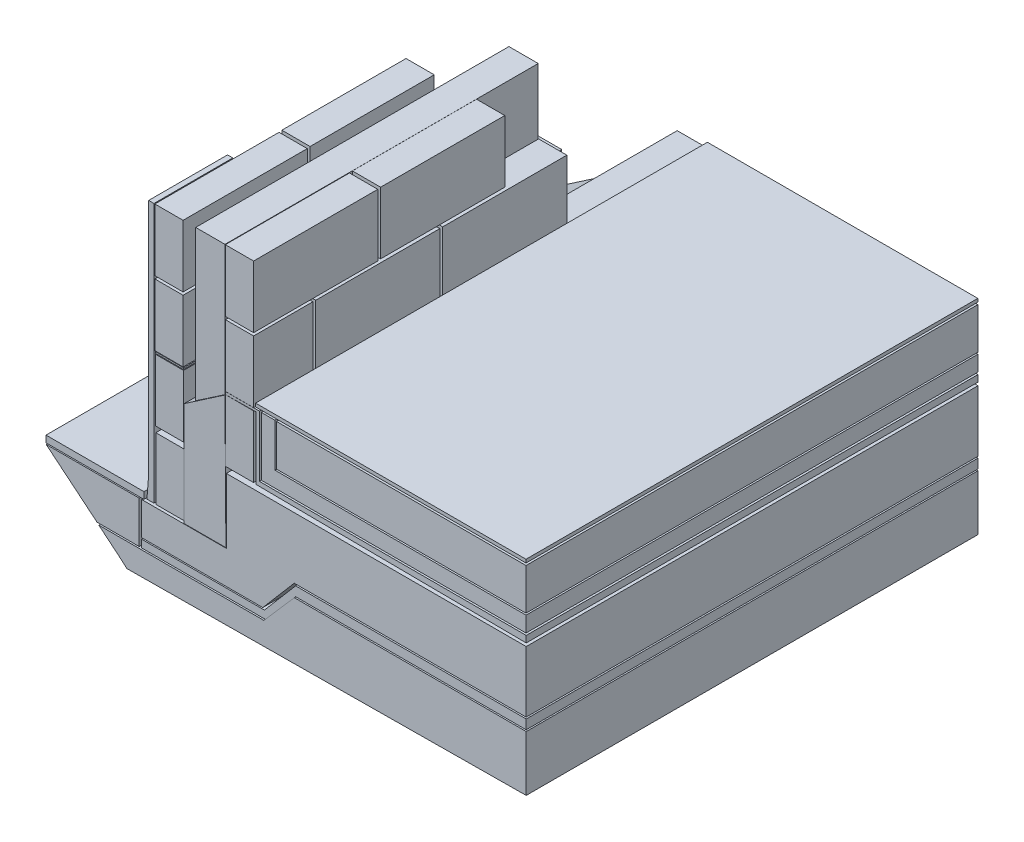
SolidWorks part; units mm, degrees
ref_plane "Front Plane" through (0, 0, 0) normal (0, 0, 1) x (1, 0, 0)
ref_plane "Top Plane" through (0, 0, 0) normal (0, 1, 0) x (1, 0, 0)
ref_plane "Right Plane" through (0, 0, 0) normal (1, 0, 0) x (0, 0, -1)
sketch "Sketch1" plane through (0, 0, 0) normal (0, 0, 1) x (1, 0, 0)
  line L0 (0, 0) -> (26.1262, -22.8216)
  line L1 (26.1262, -22.8216) -> (1435.8063, -11.4108)
  line L2 (1435.8063, 184.6868) -> (1440.9992, 184.6868)
  line L3 (1435.8063, 184.6868) -> (619.4928, 184.6868)
  line L4 (619.4928, 184.6868) -> (511.4023, 60.9451)
  line L5 (511.4023, 60.9451) -> (-73.6897, 60.9451)
  line L6 (-73.6897, 60.9451) -> (0, 0)
  line L7 (1440.9992, 184.6868) -> (1440.9992, -11.4108)
  line L8 (1440.9992, -11.4108) -> (1435.8063, -11.4108)
extrude "Extrude1" add sketch "Sketch1" against normal blind 1601
sketch "Sketch6" plane through (0, 0, 0) normal (0, 0, 1) x (1, 0, 0)
  line L0 (1440.9992, 228.8878) -> (1440.9992, 445.5033)
  line L1 (1440.9992, 445.5033) -> (378.3669, 445.5033)
  line L2 (378.3669, 445.5033) -> (378.3669, 215.5033)
  line L3 (378.3669, 215.5033) -> (78.3669, 215.5033)
  line L4 (78.3669, 215.5033) -> (78.3669, 98.3177)
  line L5 (78.3669, 98.3177) -> (507.434, 98.3177)
  line L6 (507.434, 98.3177) -> (618.9465, 228.8878)
  line L7 (618.9465, 228.8878) -> (1440.9992, 228.8878)
  line L8 (1440.9992, -11.4108) -> (1440.9992, 184.6868) construction
  dimension "D1" = 230
  dimension "D2" = 300
  dimension "D3" = 216.6155
extrude "Extrude4" add sketch "Sketch6" against normal up to vertex (1601 mm away) separate body
sketch "Sketch7" plane through (0, 0, 0) normal (0, 0, 1) x (1, 0, 0)
  line L0 (78.3669, 93.569) -> (513.2966, 93.569)
  line L1 (513.2966, 93.569) -> (624.0551, 223.2375)
  line L2 (624.0551, 223.2375) -> (1440.9992, 223.2375)
  line L3 (1440.9992, 223.2375) -> (1440.9992, 190.0192)
  line L4 (1440.9992, 190.0192) -> (624.0551, 190.0192)
  line L5 (624.0551, 190.0192) -> (518.7637, 66.7513)
  line L6 (518.7637, 66.7513) -> (78.3669, 66.7513)
  line L7 (78.3669, 66.7513) -> (78.3669, 93.569)
  line L9 (1440.9992, -11.4108) -> (1440.9992, 184.6868) construction
  line L10 (78.3669, 215.5033) -> (78.3669, 98.3177) construction
extrude "Extrude5" add sketch "Sketch7" against normal up to vertex (1601 mm away) separate body
sketch "Sketch8" plane through (0, 0, 0) normal (0, 0, 1) x (1, 0, 0)
  line L0 (378.3669, 215.5033) -> (78.3669, 215.5033) construction
  line L1 (128.3669, 445.5033) -> (228.3669, 445.5033)
  line L2 (128.3669, 445.5033) -> (128.3669, 225.5033)
  line L3 (128.3669, 225.5033) -> (228.3669, 225.5033)
  line L4 (228.3669, 445.5033) -> (228.3669, 225.5033)
  line L5 (378.3669, 445.5033) -> (378.3669, 215.5033) construction
  dimension "D1" = 100
  dimension "D2" = 220
  dimension "D3" = 10
  dimension "D4" = 150
extrude "Extrude6" add sketch "Sketch8" against normal blind 210 separate body
sketch "Sketch9" plane through (0, 0, 0) normal (0, 0, 1) x (1, 0, 0)
  line L1 (126.7181, 465.6969) -> (226.7181, 465.6969)
  line L2 (126.7181, 465.6969) -> (126.7181, 685.6969)
  line L3 (126.7181, 685.6969) -> (226.7181, 685.6969)
  line L4 (226.7181, 465.6969) -> (226.7181, 685.6969)
  line L5 (375.0647, 465.6969) -> (475.0647, 465.6969)
  line L6 (375.0647, 465.6969) -> (375.0647, 685.6969)
  line L7 (375.0647, 685.6969) -> (475.0647, 685.6969)
  line L8 (475.0647, 465.6969) -> (475.0647, 685.6969)
  dimension "D1" = 220
  dimension "D2" = 100
  dimension "D3" = 100
  dimension "D4" = 220
extrude "Extrude7" add sketch "Sketch9" against normal blind 440 separate body
sketch "Sketch10" plane through (0, 0, 0) normal (0, 0, 1) x (1, 0, 0)
  line L0 (226.7181, 685.6969) -> (126.7181, 685.6969) construction
  line L1 (125.1519, 695.6969) -> (225.1519, 695.6969)
  line L2 (125.1519, 695.6969) -> (125.1519, 915.6969)
  line L3 (125.1519, 915.6969) -> (225.1519, 915.6969)
  line L4 (225.1519, 695.6969) -> (225.1519, 915.6969)
  line L5 (375.0647, 695.6969) -> (475.0647, 695.6969)
  line L6 (375.0647, 695.6969) -> (375.0647, 915.6969)
  line L7 (375.0647, 915.6969) -> (475.0647, 915.6969)
  line L8 (475.0647, 695.6969) -> (475.0647, 915.6969)
  line L9 (475.0647, 685.6969) -> (375.0647, 685.6969) construction
  line L10 (475.0647, 465.6969) -> (475.0647, 685.6969) construction
  dimension "D1" = 100
  dimension "D2" = 220
  dimension "D3" = 220
  dimension "D4" = 100
  dimension "D5" = 10
  dimension "D6" = 10
extrude "Extrude8" add sketch "Sketch10" against normal blind 210 separate body
sketch "Sketch11" plane through (0, 0, 0) normal (0, 0, 1) x (1, 0, 0)
  line L0 (225.1519, 915.6969) -> (125.1519, 915.6969) construction
  line L1 (125.1519, 925.6969) -> (225.1519, 925.6969)
  line L2 (125.1519, 925.6969) -> (125.1519, 1145.6969)
  line L3 (125.1519, 1145.6969) -> (225.1519, 1145.6969)
  line L4 (225.1519, 925.6969) -> (225.1519, 1145.6969)
  line L5 (374.776, 925.6969) -> (474.776, 925.6969)
  line L6 (374.776, 925.6969) -> (374.776, 1145.6969)
  line L7 (374.776, 1145.6969) -> (474.776, 1145.6969)
  line L8 (474.776, 925.6969) -> (474.776, 1145.6969)
  line L9 (475.0647, 915.6969) -> (375.0647, 915.6969) construction
  dimension "D1" = 220
  dimension "D2" = 100
  dimension "D3" = 100
  dimension "D4" = 220
  dimension "D5" = 10
  dimension "D6" = 10
extrude "Extrude9" add sketch "Sketch11" against normal blind 440 separate body
sketch "Sketch12" plane through (128.3669, 0, 0) normal (-1, 0, 0) x (0, 0, 1)
  line L0 (-1601, 445.5033) -> (0, 445.5033) construction
  line L1 (-220, 445.5033) -> (-660, 445.5033)
  line L2 (-220, 445.5033) -> (-220, 225.5033)
  line L3 (-220, 225.5033) -> (-660, 225.5033)
  line L4 (-660, 445.5033) -> (-660, 225.5033)
  line L5 (-210, 445.5033) -> (-210, 225.5033) construction
  line L6 (-670, 445.5033) -> (-1110, 445.5033)
  line L7 (-670, 445.5033) -> (-670, 225.5033)
  line L8 (-670, 225.5033) -> (-1110, 225.5033)
  line L9 (-1110, 445.5033) -> (-1110, 225.5033)
  point P10 (-210, 335.5033)
  dimension "D1" = 440
  dimension "D2" = 220
  dimension "D3" = 10
  dimension "D4" = 440
  dimension "D5" = 220
  dimension "D6" = 10
extrude "Extrude10" add sketch "Sketch12" against normal blind 100 separate body
sketch "Sketch13" plane through (126.7181, 0, 0) normal (-1, 0, 0) x (0, 0, 1)
  line L0 (-440, 685.6969) -> (-440, 465.6969) construction
  line L1 (-450, 685.9842) -> (-890, 685.9842)
  line L2 (-450, 685.9842) -> (-450, 465.9842)
  line L3 (-450, 465.9842) -> (-890, 465.9842)
  line L4 (-890, 685.9842) -> (-890, 465.9842)
  line L5 (-900, 685.6969) -> (-1340, 685.6969)
  line L6 (-900, 685.6969) -> (-900, 465.6969)
  line L7 (-900, 465.6969) -> (-1340, 465.6969)
  line L8 (-1340, 685.6969) -> (-1340, 465.6969)
  line L9 (-440, 465.6969) -> (0, 465.6969) construction
  dimension "D1" = 440
  dimension "D2" = 220
  dimension "D3" = 220
  dimension "D4" = 440
  dimension "D5" = 10
  dimension "D6" = 10
extrude "Extrude11" add sketch "Sketch13" against normal blind 100 separate body
sketch "Sketch14" plane through (128.3669, 0, 0) normal (-1, 0, 0) x (0, 0, 1)
  line L0 (-1601, 445.5033) -> (0, 445.5033) construction
  line L1 (-1120, 445.5033) -> (-1560, 445.5033)
  line L2 (-1120, 445.5033) -> (-1120, 225.5033)
  line L3 (-1120, 225.5033) -> (-1560, 225.5033)
  line L4 (-1560, 445.5033) -> (-1560, 225.5033)
  line L5 (-1110, 445.5033) -> (-1110, 225.5033) construction
  dimension "D1" = 220
  dimension "D2" = 440
  dimension "D3" = 10
extrude "Extrude12" add sketch "Sketch14" against normal blind 100 separate body
sketch "Sketch15" plane through (125.1519, 0, 0) normal (-1, 0, 0) x (0, 0, 1)
  line L0 (-210, 915.6969) -> (-210, 695.6969) construction
  line L1 (-220, 915.274) -> (-660, 915.274)
  line L2 (-220, 915.274) -> (-220, 695.274)
  line L3 (-220, 695.274) -> (-660, 695.274)
  line L4 (-660, 915.274) -> (-660, 695.274)
  line L5 (-670, 915.5026) -> (-1110, 915.5026)
  line L6 (-670, 915.5026) -> (-670, 695.5026)
  line L7 (-670, 695.5026) -> (-1110, 695.5026)
  line L8 (-1110, 915.5026) -> (-1110, 695.5026)
  dimension "D1" = 220
  dimension "D2" = 440
  dimension "D3" = 440
  dimension "D4" = 220
  dimension "D5" = 10
  dimension "D6" = 10
extrude "Extrude13" add sketch "Sketch15" against normal blind 100 separate body
sketch "Sketch16" plane through (125.1519, 0, 0) normal (-1, 0, 0) x (0, 0, 1)
  line L0 (-440, 1145.6969) -> (-440, 925.6969) construction
  line L1 (-450, 1147.2011) -> (-890, 1147.2011)
  line L2 (-450, 1147.2011) -> (-450, 927.2011)
  line L3 (-450, 927.2011) -> (-890, 927.2011)
  line L4 (-890, 1147.2011) -> (-890, 927.2011)
  dimension "D1" = 440
  dimension "D2" = 220
  dimension "D3" = 10
extrude "Extrude14" add sketch "Sketch16" against normal blind 100 separate body
sketch "Sketch17" plane through (475.0647, 0, 0) normal (1, 0, 0) x (0, 0, -1)
  line L0 (890, 465.9842) -> (450, 465.9842) construction
  line L1 (450, 685.9842) -> (890, 685.9842)
  line L2 (450, 685.9842) -> (450, 465.9842)
  line L3 (450, 465.9842) -> (890, 465.9842)
  line L4 (890, 685.9842) -> (890, 465.9842)
  line L5 (440, 925.6969) -> (440, 1145.6969) construction
  line L6 (1340, 685.6969) -> (900, 685.6969)
  line L7 (1340, 685.6969) -> (1340, 465.6969)
  line L8 (1340, 465.6969) -> (900, 465.6969)
  line L9 (900, 685.6969) -> (900, 465.6969)
  line L10 (1110, 915.5026) -> (670, 915.5026)
  line L11 (1110, 915.5026) -> (1110, 695.5026)
  line L12 (1110, 695.5026) -> (670, 695.5026)
  line L13 (670, 915.5026) -> (670, 695.5026)
  line L14 (660, 915.274) -> (220, 915.274)
  line L15 (660, 915.274) -> (660, 695.274)
  line L16 (660, 695.274) -> (220, 695.274)
  line L17 (220, 915.274) -> (220, 695.274)
  line L18 (0, 915.6969) -> (210, 915.6969)
  line L19 (0, 915.6969) -> (0, 695.6969)
  line L20 (0, 695.6969) -> (210, 695.6969)
  line L21 (210, 915.6969) -> (210, 695.6969)
  line L22 (0, 1145.6969) -> (440, 1145.6969)
  line L23 (0, 1145.6969) -> (0, 925.6969)
  line L24 (0, 925.6969) -> (440, 925.6969)
  line L25 (440, 1145.6969) -> (440, 925.6969)
  line L27 (890, 1147.2011) -> (450, 1147.2011)
  line L28 (890, 1147.2011) -> (890, 927.2011)
  line L29 (890, 927.2011) -> (450, 927.2011)
  line L30 (450, 1147.2011) -> (450, 927.2011)
extrude "Extrude15" add sketch "Sketch17" against normal blind 100
sketch "Sketch18" plane through (0, 0, 0) normal (0, 0, 1) x (1, 0, 0)
  line L0 (69.7561, 66.7513) -> (69.7561, 215.2631)
  line L1 (69.7561, 215.2631) -> (-260.0365, 215.2631)
  line L4 (69.7561, 66.7513) -> (-79.7988, 66.7513)
  line L5 (-79.7988, 66.7513) -> (-260.0365, 215.2631)
extrude "Extrude19" add sketch "Sketch18" against normal up to vertex (1601 mm away) separate body
sketch "Sketch19" plane through (0, 0, 0) normal (0, 0, 1) x (1, 0, 0)
  line L0 (1440.9992, 456.5257) -> (483.0875, 464.3663)
  line L1 (483.0875, 464.3663) -> (483.0875, 626.7546)
  line L2 (483.0875, 626.7546) -> (483.0875, 686.9511)
  line L3 (495.4208, 626.7546) -> (495.4208, 479.7829)
  line L4 (495.4208, 479.7829) -> (1440.9992, 479.7829)
  line L5 (1440.9992, 479.7829) -> (1440.9992, 456.5257)
  line L6 (483.0875, 686.9511) -> (375.0647, 685.9842)
  line L7 (375.0647, 685.9842) -> (475.0647, 685.9842) construction
  line L8 (375.0647, 685.9842) -> (375.0647, 695.274)
  line L9 (375.0647, 695.274) -> (475.0647, 695.274) construction
  line L10 (375.0647, 695.274) -> (495.4208, 695.274)
  line L11 (495.4208, 695.274) -> (495.4208, 626.7546)
extrude "Extrude20" add sketch "Sketch19" against normal up to vertex (1601 mm away) separate body
sketch "Sketch21" plane through (0, 0, 0) normal (0, 0, 1) x (1, 0, 0)
  line L0 (502.237, 694.7532) -> (502.237, 486.5906)
  line L1 (502.237, 486.5906) -> (1440.3276, 486.5906)
  line L2 (1440.3276, 486.5906) -> (1440.3276, 541.5816)
  line L3 (1440.3276, 541.5816) -> (550.4417, 541.5816)
  line L4 (550.4417, 541.5816) -> (550.4417, 694.7532)
  line L5 (550.4417, 694.7532) -> (502.237, 694.7532)
extrude "Extrude22" add sketch "Sketch21" against normal up to vertex (1601 mm away) separate body
sketch "Sketch22" plane through (0, 0, 0) normal (0, 0, 1) x (1, 0, 0)
  line L1 (556.0644, 693.8804) -> (1440.3276, 693.8804)
  line L2 (556.0644, 693.8804) -> (556.0644, 547.6191)
  line L3 (556.0644, 547.6191) -> (1440.3276, 547.6191)
  line L4 (1440.3276, 693.8804) -> (1440.3276, 547.6191)
extrude "Extrude23" add sketch "Sketch22" against normal up to vertex (1601 mm away) separate body
sketch "Sketch23" plane through (0, 0, 0) normal (0, 0, 1) x (1, 0, 0)
  line L0 (126.9611, 693.8146) -> (226.6355, 693.8146)
  line L1 (226.6355, 688.5559) -> (126.9611, 688.5559)
  line L2 (126.9611, 688.5559) -> (126.9611, 693.8146)
  line L3 (226.6355, 693.8146) -> (226.6355, 688.5559)
extrude "Extrude24" add sketch "Sketch23" against normal up to vertex (1340 mm away) separate body
sketch "Sketch24" plane through (0, 0, 0) normal (0, 0, 1) x (1, 0, 0)
  line L0 (373.4692, 683.6938) -> (376.8644, 216.962)
  line L1 (376.8644, 216.962) -> (229.0389, 216.962)
  line L2 (229.0389, 216.962) -> (229.0389, 585.0243)
  line L3 (229.0389, 585.0243) -> (373.4692, 683.6938)
extrude "Extrude25" add sketch "Sketch24" against normal up to vertex (1340 mm away) separate body
sketch "Sketch25" plane through (0, 0, 0) normal (0, 0, 1) x (1, 0, 0)
  line L0 (373.6168, 684.8576) -> (373.6168, 1146.1606)
  line L1 (373.6168, 1146.1606) -> (269.7986, 1146.1606)
  line L2 (269.7986, 1146.1606) -> (269.7986, 614.1422)
  line L3 (269.7986, 614.1422) -> (373.6168, 684.8576)
extrude "Extrude26" add sketch "Sketch25" against normal up to vertex (1110 mm away) separate body
sketch "Sketch27" plane through (0, 0, 0) normal (0, 0, 1) x (1, 0, 0)
  line L0 (121.9766, 1145.7702) -> (121.9766, 225.9237)
  line L1 (121.9766, 225.9237) -> (96.9728, 225.9237)
  line L2 (96.9728, 225.9237) -> (103.2208, 304.0239)
  line L3 (103.2208, 304.0239) -> (103.2208, 1145.7702)
  line L4 (103.2208, 1145.7702) -> (121.9766, 1145.7702)
extrude "Extrude29" add sketch "Sketch27" against normal blind 559 separate body
sketch "Sketch30" plane through (103.2208, 0, 0) normal (-1, 0, 0) x (0, 0, 1)
  line L0 (-559, 1145.7702) -> (-279.5, 1145.7702)
  line L1 (-559, 1145.7702) -> (0, 1145.7702) construction
  line L2 (-559, 225.9237) -> (0, 225.9237) construction
  line L3 (-470.8496, 225.9237) -> (-559, 225.9237)
  line L4 (-559, 225.9237) -> (-559, 1145.7702)
  spline S0 degree 3 poles (-279.5, 1145.7702) (-3.1177, 751.9861) (-620.5924, 618.2023) (-470.8496, 225.9237) knots 0 0 0 0 1 1 1 1
extrude "Extrude33" cut sketch "Sketch30" against normal mid plane 43
sketch "Sketch31" plane through (0, 0, 0) normal (0, 0, 1) x (1, 0, 0)
  line L1 (-260.6289, 219.8093) -> (86.3841, 219.8093)
  line L2 (-260.6289, 219.8093) -> (-260.6289, 243.6416)
  line L3 (-260.6289, 243.6416) -> (86.3841, 243.6416)
  line L4 (86.3841, 219.8093) -> (86.3841, 243.6416)
extrude "Extrude34" add sketch "Sketch31" against normal up to vertex (1601 mm away) separate body
sketch "Sketch32" plane through (0, 0, 0) normal (0, 0, 1) x (1, 0, 0)
  line L1 (482.0548, 701.5128) -> (1440.3276, 701.5128)
  line L2 (482.0548, 701.5128) -> (482.0548, 713.1809)
  line L3 (482.0548, 713.1809) -> (1440.3276, 713.1809)
  line L4 (1440.3276, 701.5128) -> (1440.3276, 713.1809)
extrude "Extrude35" add sketch "Sketch32" against normal up to vertex (1601 mm away) separate body
